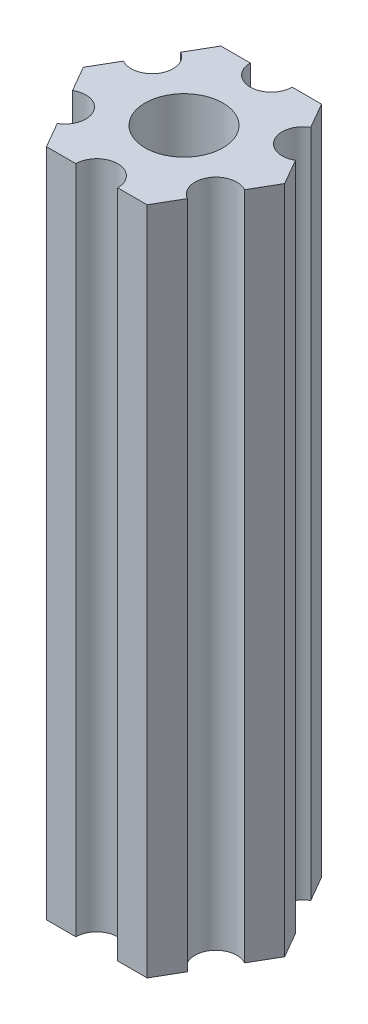
SolidWorks part; units mm, degrees
material "Churro - 6005A-T61"
ref_plane "Plano frontal" through (0, 0, 0) normal (0, 0, 1) x (1, 0, 0)
ref_plane "Plano superior" through (0, 0, 0) normal (0, 1, 0) x (1, 0, 0)
ref_plane "Plano direito" through (0, 0, 0) normal (1, 0, 0) x (0, 0, -1)
ref_plane "Plano1" through (0, 85, 0) normal (0, 1, 0) x (1, 0, 0)
sketch "Esboço1" plane through (0, 85, 0) normal (0, 1, 0) x (1, 0, 0)
  line L0 (6.1627, -1.826) -> (7.2169, 0)
  line L1 (7.2169, 0) -> (6.1627, 1.826)
  line L2 (4.6627, 4.424) -> (3.6084, 6.25)
  line L3 (3.6084, 6.25) -> (1.5, 6.25)
  line L4 (-1.5, 6.25) -> (-3.6084, 6.25)
  line L5 (-3.6084, 6.25) -> (-4.6627, 4.424)
  line L6 (-6.1627, 1.826) -> (-7.2169, 0)
  line L7 (-7.2169, 0) -> (-6.1627, -1.826)
  line L8 (-4.6627, -4.424) -> (-3.6084, -6.25)
  line L9 (-3.6084, -6.25) -> (-1.5, -6.25)
  line L10 (1.5, -6.25) -> (3.6084, -6.25)
  line L11 (3.6084, -6.25) -> (4.6627, -4.424)
  arc A0 (6.1627, 1.826) -> (4.6627, 4.424) centre (5.4127, 3.125) cw
  arc A1 (1.5, 6.25) -> (-1.5, 6.25) centre (0, 6.25) cw
  arc A2 (-4.6627, 4.424) -> (-6.1627, 1.826) centre (-5.4127, 3.125) cw
  arc A3 (-6.1627, -1.826) -> (-4.6627, -4.424) centre (-5.4127, -3.125) cw
  arc A4 (-1.5, -6.25) -> (1.5, -6.25) centre (0, -6.25) cw
  arc A5 (4.6627, -4.424) -> (6.1627, -1.826) centre (5.4127, -3.125) cw
  circle A6 centre (0, 0) radius 2.79
extrude "Ressalto-extrusão1" add sketch "Esboço1" against normal blind 48
